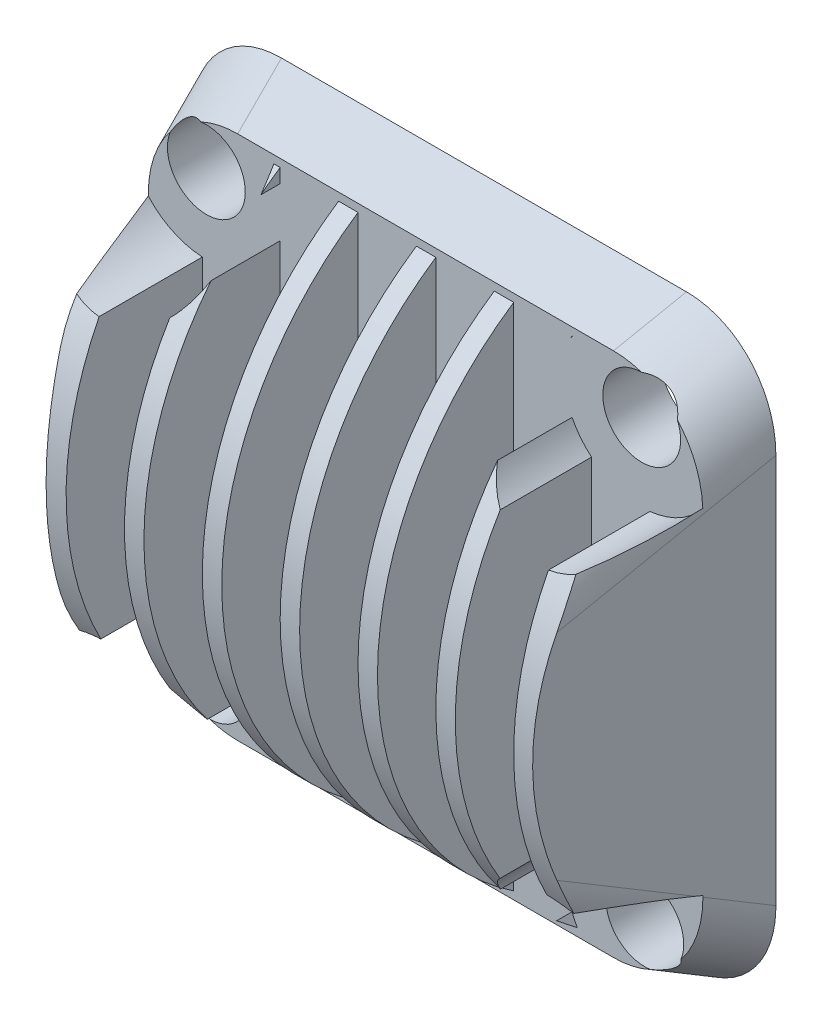
SolidWorks part; units mm, degrees
ref_plane "Front Plane" through (0, 0, 0) normal (0, 0, 1) x (1, 0, 0)
ref_plane "Top Plane" through (0, 0, 0) normal (0, 1, 0) x (1, 0, 0)
ref_plane "Right Plane" through (0, 0, 0) normal (1, 0, 0) x (0, 0, -1)
sketch "Sketch1" plane through (0, 0, 0) normal (0, 0, 1) x (1, 0, 0)
  line L1 (-15, 15) -> (15, 15)
  line L2 (-15, 15) -> (-15, -15)
  line L3 (-15, -15) -> (15, -15)
  line L4 (15, 15) -> (15, -15)
  line L5 (-15, 15) -> (15, -15) construction
  line L6 (-15, -15) -> (15, 15) construction
  point P0 (0, 0)
  dimension "D1" = 30
  dimension "D2" = 30
ref_plane "Plane1" through (0, 0, 10) normal (0, 0, 1) x (1, 0, 0)
sketch "Sketch2" plane through (0, 0, 10) normal (0, 0, 1) x (1, 0, 0)
  line L1 (-12.5, 10) -> (12.5, 10)
  line L2 (-12.5, 10) -> (-12.5, -10)
  line L3 (-12.5, -10) -> (12.5, -10)
  line L4 (12.5, 10) -> (12.5, -10)
  line L5 (-12.5, 10) -> (12.5, -10) construction
  line L6 (-12.5, -10) -> (12.5, 10) construction
  point P0 (0, 0)
  dimension "D1" = 20
  dimension "D2" = 25
loft "Loft1" add profiles "Sketch2", "Sketch1"
fillet "Fillet1" radius 5 4 edges
sketch "Sketch3" plane through (0, 0, 0) normal (0, 1, 0) x (1, 0, 0)
  line L0 (-10.4051, 0) -> (-15, 0) construction
  line L1 (-11.4726, -3) -> (-8.4726, -3)
  line L2 (-11.4726, -3) -> (-11.4726, -12.4269)
  line L3 (-11.4726, -12.4269) -> (-8.4726, -12.4269)
  line L4 (-8.4726, -3) -> (-8.4726, -12.4269)
  dimension "D1" = 3
  dimension "D2" = 3
extrude "Cut-Extrude1" cut sketch "Sketch3" against normal through all both and the other way through all
pattern_linear "LPattern3" count 6 spacing 4 along (1, 0, 0) of "Cut-Extrude1"
sketch "Sketch4" plane through (0, 0, 0) normal (1, 0, 0) x (0, 0, -1)
  line L0 (-3, 13.0959) -> (-3, 16.033)
  line L1 (-3, 16.033) -> (-15.0603, 16.033)
  line L2 (-15.0603, 16.033) -> (-15.0603, -14.5928)
  line L3 (-15.0603, -14.5928) -> (-3, -14.5928)
  line L4 (-3, -14.5928) -> (-3, -13.0959)
  arc A0 (-3, 13.0959) -> (-3, -13.0959) centre (5.7501, 0) ccw
extrude "Cut-Extrude4" cut sketch "Sketch4" against normal through all both and the other way through all contours L2 L3 L4 A0 L0 L1
sketch "Sketch5" plane through (0, 0, 0) normal (0, 0, -1) x (-1, 0, 0)
  line L0 (0, 0) -> (-15.2663, 15.4865) construction
  circle A0 centre (0, 0) radius 15.82
  circle A1 centre (-11.1051, 11.2653) radius 2
  point P3 (-11.1051, 11.2653)
  dimension "D1" = 31.64
  dimension "D2" = 4
extrude "Cut-Extrude5" cut sketch "Sketch5" against normal through all both and the other way through all contours A0 L0 A1 | A1 L0 A0 | L0 A1 A0 | L0 A0 A1
sketch "Sketch6" plane through (0, 0, 0) normal (0, 0, -1) x (-1, 0, 0)
  circle A0 centre (0, 0) radius 12.5
  dimension "D1" = 25
extrude "Cut-Extrude6" cut sketch "Sketch6" against normal blind 1 contours A0
sketch "Sketch9" plane through (0, 0, 3) normal (0, 0, 1) x (1, 0, 0)
  circle A0 centre (11.1051, 11.2653) radius 4
  dimension "D1" = 8
extrude "Cut-Extrude9" cut sketch "Sketch9" along normal blind 14 contours A0
pattern_circular "CirPattern2" count 4 over 360 about axis through (0, 0, 0) along (0, 0, 1) of "Cut-Extrude9", "Cut-Extrude5"
